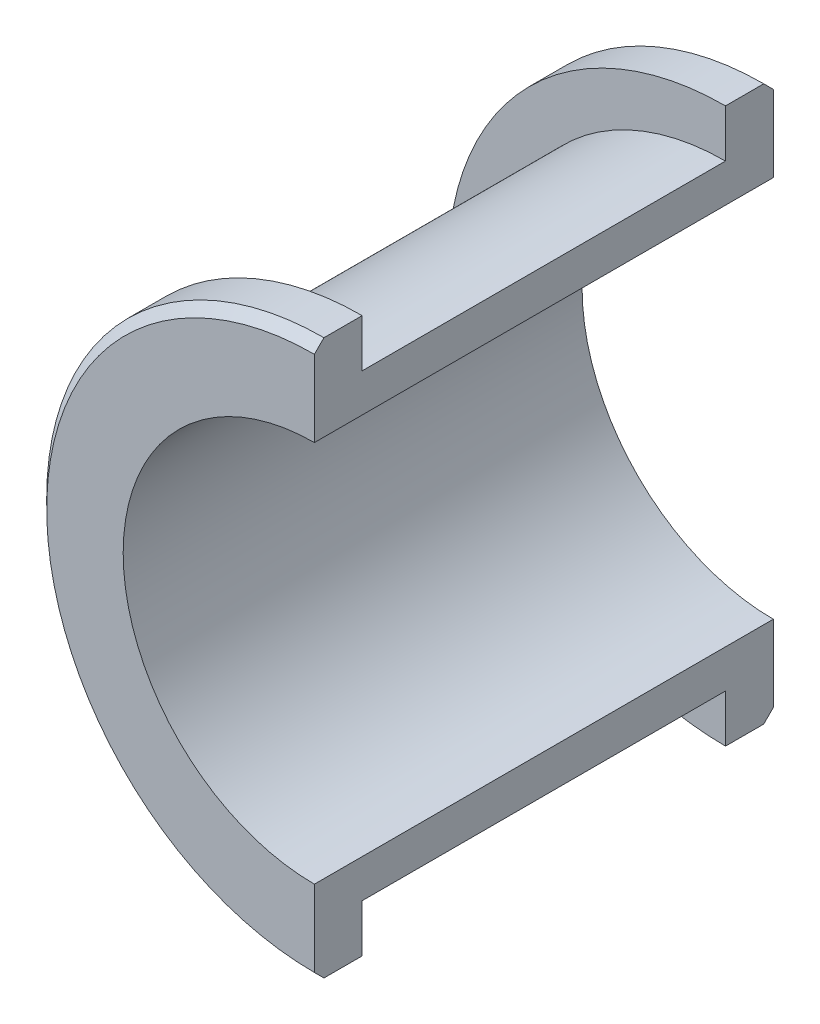
SolidWorks part; units mm, degrees
material "Бронза"
ref_plane "Спереди" through (0, 0, 0) normal (0, 0, 1) x (1, 0, 0)
ref_plane "Сверху" through (0, 0, 0) normal (0, 1, 0) x (1, 0, 0)
ref_plane "Справа" through (0, 0, 0) normal (1, 0, 0) x (0, 0, -1)
sketch "Эскиз1" plane through (0, 0, 0) normal (0, 0, 1) x (1, 0, 0)
  circle A0 centre (0, 0) radius 20
  circle A1 centre (0, 0) radius 24
  dimension "D1" = 40
  dimension "D2" = 48
extrude "Бобышка-Вытянуть1" add sketch "Эскиз1" along normal blind 24
sketch "Эскиз2" plane through (0, 0, 24) normal (0, 0, 1) x (1, 0, 0)
  circle A0 centre (0, 0) radius 29
  circle A1 centre (0, 0) radius 24
  circle A2 centre (0, 0) radius 24
  dimension "D2" = 58
  dimension "D1" = 0
extrude "Бобышка-Вытянуть2" add sketch "Эскиз2" against normal blind 5
mirror "Зеркальное отражение1" about plane through (0, 0, 0) normal (0, 0, 1) of bodies 106
sketch "Эскиз3" plane through (0, 0, 24) normal (0, 0, 1) x (1, 0, 0)
  line L1 (0, -29) -> (29, -29)
  line L2 (0, -29) -> (0, 29)
  line L3 (0, 29) -> (29, 29)
  line L4 (29, -29) -> (29, 29)
  circle A0 centre (0, 0) radius 29 construction
extrude "Вырез-Вытянуть1" cut sketch "Эскиз3" against normal through all
chamfer "Фаска1" distance 1 angle 45 2 edges at (-29, 0, -24) (-29, 0, 24)
